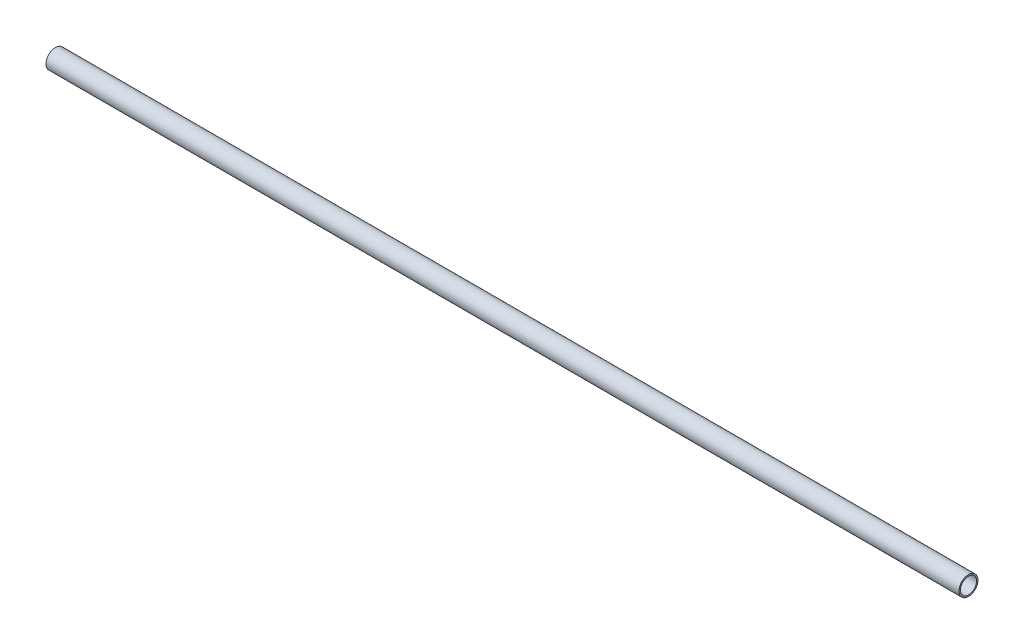
SolidWorks part; units mm, degrees
ref_plane "Front Plane" through (0, 0, 0) normal (0, 0, 1) x (1, 0, 0)
ref_plane "Top Plane" through (0, 0, 0) normal (0, 1, 0) x (1, 0, 0)
ref_plane "Right Plane" through (0, 0, 0) normal (1, 0, 0) x (0, 0, -1)
sketch "Sketch1" plane through (0, 0, 0) normal (1, 0, 0) x (0, 0, -1)
  circle A0 centre (0, 0) radius 10.795
  circle A1 centre (0, 0) radius 12.7
  dimension "D1" = 21.59
  dimension "D2" = 25.4
extrude "Boss-Extrude1" add sketch "Sketch1" along normal blind 1219.2
sketch "Sketch2" plane through (0, 0, 0) normal (0, 0, 1) x (1, 0, 0)
  line L0 (0, 0) -> (50.8, 0) construction
  line L1 (50.8, 0) -> (101.6, 0) construction
  circle A0 centre (50.8, 0) radius 1.5875
  circle A1 centre (101.6, 0) radius 1.5875
  circle A2 centre (152.4, 0) radius 1.5875
  circle A3 centre (203.2, 0) radius 1.5875
  circle A4 centre (254, 0) radius 1.5875
  circle A5 centre (304.8, 0) radius 1.5875
  circle A6 centre (355.6, 0) radius 1.5875
  circle A7 centre (406.4, 0) radius 1.5875
  circle A8 centre (457.2, 0) radius 1.5875
  circle A9 centre (508, 0) radius 1.5875
  circle A10 centre (558.8, 0) radius 1.5875
  circle A11 centre (609.6, 0) radius 1.5875
  circle A12 centre (660.4, 0) radius 1.5875
  circle A13 centre (711.2, 0) radius 1.5875
  circle A14 centre (762, 0) radius 1.5875
  circle A15 centre (812.8, 0) radius 1.5875
  circle A16 centre (863.6, 0) radius 1.5875
  circle A17 centre (914.4, 0) radius 1.5875
  circle A18 centre (965.2, 0) radius 1.5875
  circle A19 centre (1016, 0) radius 1.5875
  circle A20 centre (1066.8, 0) radius 1.5875
  circle A21 centre (1117.6, 0) radius 1.5875
  circle A22 centre (1168.4, 0) radius 1.5875
  dimension "D2" = 3.175
  dimension "D1" = 50.8
  dimension "D4" = 50.8
  dimension "D3" = 23
extrude "Cut-Extrude1" cut sketch "Sketch2" against normal blind 1219.2
